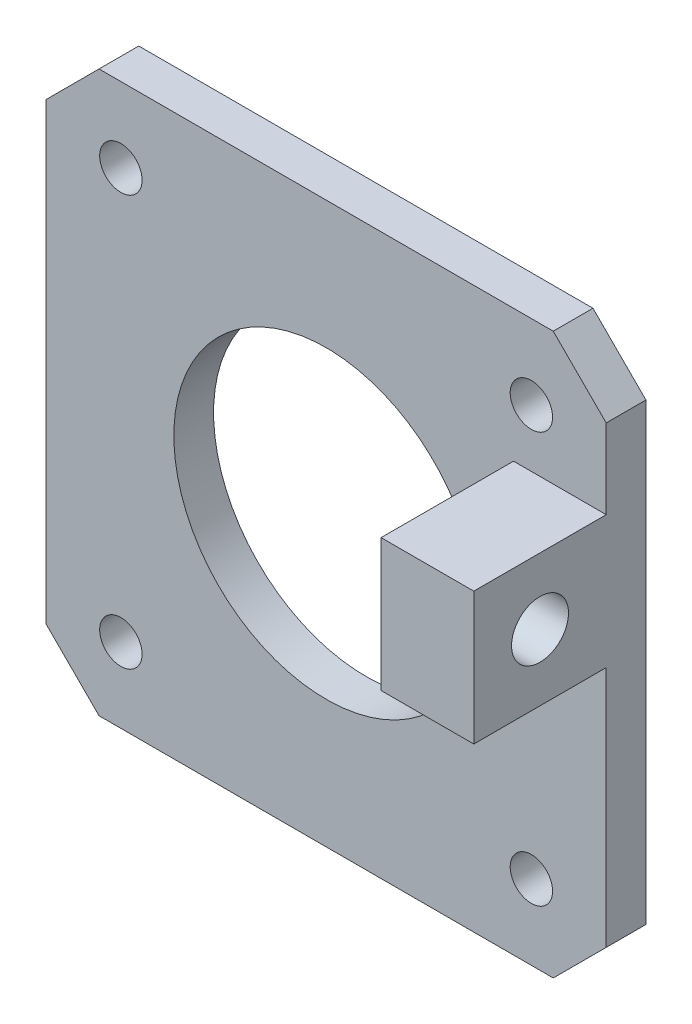
SolidWorks part; units mm, degrees
ref_plane "Front Plane" through (0, 0, 0) normal (0, 0, 1) x (1, 0, 0)
ref_plane "Top Plane" through (0, 0, 0) normal (0, 1, 0) x (1, 0, 0)
ref_plane "Right Plane" through (0, 0, 0) normal (1, 0, 0) x (0, 0, -1)
sketch "Croquis1" plane through (0, 0, 0) normal (0, 0, 1) x (1, 0, 0)
  line L1 (21.15, -17.15) -> (17.15, -21.15) construction
  line L2 (17.15, -21.15) -> (-17.15, -21.15) construction
  line L3 (-17.15, -21.15) -> (-21.15, -17.15) construction
  line L4 (-21.15, -17.15) -> (-21.15, 17.15) construction
  line L5 (17.15, 21.15) -> (16.7358, 20.15)
  line L6 (16.7358, 20.15) -> (20.15, 16.7358)
  line L7 (20.15, 16.7358) -> (21.15, 17.15)
  line L8 (21.15, 17.15) -> (17.15, 21.15)
  line L12 (21.15, 17.15) -> (17.15, 21.15)
  line L13 (-21.15, 17.15) -> (-17.15, 21.15) construction
  line L14 (-17.15, 21.15) -> (17.15, 21.15) construction
  line L15 (21.15, 17.15) -> (21.15, -17.15) construction
  line L16 (21.15, -17.15) -> (17.15, -21.15)
  line L17 (17.15, -21.15) -> (-17.15, -21.15)
  line L18 (-17.15, -21.15) -> (-21.15, -17.15)
  line L19 (-21.15, -17.15) -> (-21.15, 17.15)
  line L20 (-21.15, 17.15) -> (-17.15, 21.15)
  line L21 (-17.15, 21.15) -> (17.15, 21.15)
  line L22 (21.15, 17.15) -> (21.15, -17.15)
  circle A0 centre (0, 0) radius 11.5 construction
  circle A1 centre (0, 0) radius 11.5
  circle A12 centre (15.5, 15.5) radius 1.6
  circle A13 centre (15.5, 15.5) radius 1.6
  circle A27 centre (15.5, -15.5) radius 1.6
  circle A28 centre (15.5, -15.5) radius 1.6
  circle A30 centre (-15.5, -15.5) radius 1.6
  circle A31 centre (-15.5, -15.5) radius 1.6
  circle A32 centre (15.5, 15.5) radius 2.75 construction
  circle A33 centre (-15.5, 15.5) radius 1.6
  circle A34 centre (-15.5, 15.5) radius 1.6
  dimension "D6" = 5.5
  dimension "D1" = 0
  dimension "D2" = 0.35
  dimension "D3" = 0.35
  dimension "D4" = 0.35
  dimension "D5" = 0.35
extrude "Saliente-Extruir1" add sketch "Croquis1" along normal blind 3
sketch "Croquis2" plane through (21.15, 0, 0) normal (1, 0, 0) x (0, 0, -1)
  line L0 (-331, 6.25) -> (-331, 6.05) construction
  line L1 (-331, 6.25) -> (-331, 6.05)
  line L2 (-331, 6.15) -> (173.6057, 6.15) construction
  line L3 (-3, -17.15) -> (-3, 17.15) construction
  line L5 (-13, 11.15) -> (-3, 11.15)
  line L6 (-13, 11.15) -> (-13, 1.15)
  line L7 (-13, 1.15) -> (-3, 1.15)
  line L8 (-3, 11.15) -> (-3, 1.15)
  line L9 (-8, 1.15) -> (-8, 11.15) construction
  line L10 (-13, 6.15) -> (-3, 6.15) construction
  circle A0 centre (-8, 6.15) radius 2.15
  circle A1 centre (-8, 6.15) radius 3.5 construction
  point P4 (-8, 6.15)
  point P9 (-3, 6.15)
  point P16 (-331, 6.15)
  line M7 (-3, 17.15) -> (-3, -17.15)
  dimension "D3" = 4.3
  dimension "D4" = 7
  dimension "D1" = 10
  dimension "D2" = 10
extrude "Saliente-Extruir2" add sketch "Croquis2" against normal blind 7 contours L6 L7 L5 A0 M7
